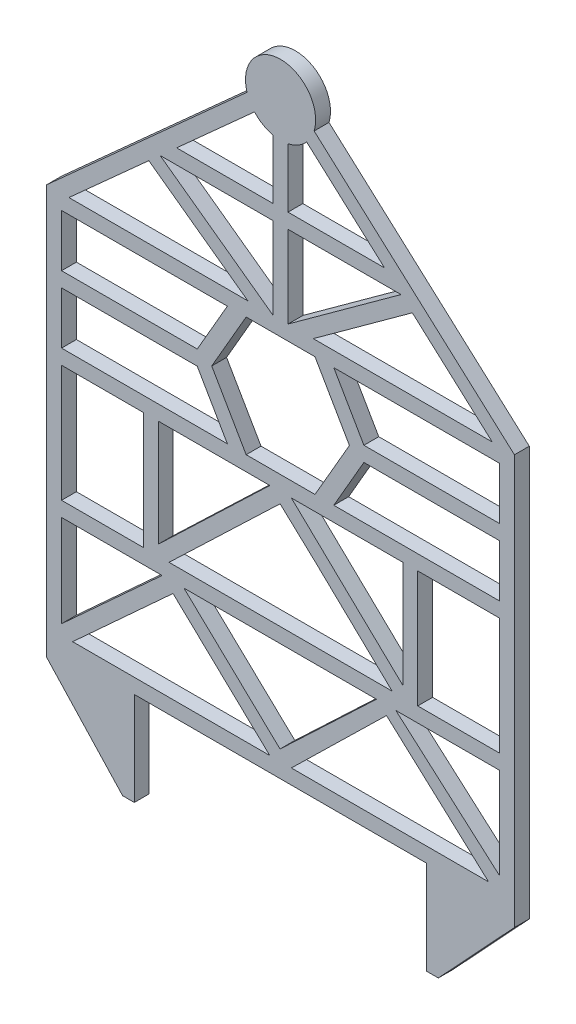
SolidWorks part; units mm, degrees
ref_plane "Front Plane" through (0, 0, 0) normal (0, 0, 1) x (1, 0, 0)
ref_plane "Top Plane" through (0, 0, 0) normal (0, 1, 0) x (1, 0, 0)
ref_plane "Right Plane" through (0, 0, 0) normal (1, 0, 0) x (0, 0, -1)
sketch "Sketch2" plane through (0, 0, 0) normal (0, 0, 1) x (1, 0, 0)
  line L0 (-135.0555, -300) -> (-125.0804, -300)
  line L1 (-126.7754, -220) -> (125.5716, -220)
  line L2 (-125.0804, -220) -> (-125.0804, -300)
  line L3 (-182.114, 120.0492) -> (182.114, 120.0492)
  line L4 (-200, 120.0492) -> (0, 300)
  line L5 (0, 300) -> (200, 120.0492)
  line L6 (-200, 120.0492) -> (-200, -220)
  line L7 (-104.6, 5.4) -> (-117.3, 5.4)
  line L8 (200, 120.0492) -> (200, -220)
  line L9 (124.9196, -220) -> (124.9196, -300)
  line L10 (58.8789, 56.3746) -> (29.4395, 107.3652)
  line L11 (29.4395, 107.3652) -> (-29.4395, 107.3652)
  line L12 (200, -230.0445) -> (134.9116, -300)
  line L13 (-29.4395, 107.3652) -> (-58.8789, 56.3746)
  line L14 (-200, -230.0445) -> (-135.0555, -300)
  line L15 (-104.6, 5.4) -> (104.6, 5.4)
  line L16 (-187.3, -107.3) -> (187.3, -107.3)
  line L17 (124.9196, -300) -> (134.9116, -300)
  line L18 (200, -220) -> (200, -230.0445)
  line L19 (-200, -220) -> (-200, -230.0445)
  line L20 (-58.8789, 56.3746) -> (-29.4395, 5.3839)
  line L21 (-29.4395, 5.3839) -> (29.4395, 5.3839)
  line L22 (187.3101, 107.3492) -> (-187.3356, 107.3492)
  line L23 (-187.3, 107.3492) -> (-187.3, -207.3409)
  line L24 (187.3, -198.4051) -> (187.3, 107.3492)
  line L25 (178.238, -207.3) -> (-178.1968, -207.3)
  line L26 (-181.0126, 120.0492) -> (0, 282.916)
  line L27 (0, 282.916) -> (181.0126, 120.0492)
  line L28 (-191.5054, 110.6082) -> (0, 282.916) construction
  line L29 (0, 282.916) -> (191.5054, 110.6082) construction
  line L31 (0, 202.9179) -> (88.9111, 202.9179)
  line L32 (0, 202.9179) -> (-88.9111, 202.9179)
  line L34 (-103.0261, 190.2179) -> (103.0261, 190.2179)
  line L37 (-6.35, 277.2025) -> (-6.35, 120.0492)
  line L38 (6.35, 277.2025) -> (6.35, 120.0492)
  line L39 (-6.35, 120.0492) -> (-103.0261, 190.2179)
  line L40 (6.35, 120.0492) -> (103.0261, 190.2179)
  line L43 (-117.3, -7.3) -> (-187.3, -7.3)
  line L44 (112.6797, 181.532) -> (27.9708, 120.0492)
  line L45 (-135.0555, -7.3) -> (-135.0555, 5.4)
  line L46 (-27.9708, 120.0492) -> (-112.6797, 181.532)
  line L47 (-117.3, -107.3) -> (-117.3, -7.3)
  line L48 (117.3, -107.3) -> (117.3, -7.3)
  line L49 (117.3, -7.3) -> (187.3, -7.3)
  line L50 (187.3, 5.4) -> (117.3, 5.4)
  line L52 (-187.3, 5.4) -> (-117.3, 5.4)
  line L53 (-117.3, 5.4) -> (-117.3, -7.3)
  line L54 (117.3, -6.6639) -> (117.3, -7.3)
  line L57 (-104.6, 5.4) -> (-104.6, -99.4267)
  line L58 (117.3, 5.4) -> (104.6, 5.4)
  line L59 (104.6, -6.7751) -> (104.6, -99.0643)
  line L60 (-187.3, -120) -> (187.3, -120)
  line L61 (-104.6, -7.3) -> (104.6, -7.3)
  line L62 (29.4395, 5.3839) -> (58.8789, 56.3746)
  line L63 (74.9313, 56.3746) -> (44.9996, 108.2179)
  line L65 (-45.5011, 107.3492) -> (-74.9313, 56.3746)
  line L66 (-74.9313, 56.3746) -> (-37.4657, -8.5179)
  line L68 (-67.7141, -80.8212) -> (-95.4109, -107.3)
  line L69 (-76.4902, -71.6414) -> (-104.6, -98.515)
  line L70 (-104.6, -98.515) -> (-9.1891, -7.3)
  line L71 (30.2421, -44.9971) -> (95.4109, -107.3)
  line L72 (39.0182, -35.8173) -> (104.6, -98.515)
  line L73 (39.0182, -35.8173) -> (9.1891, -7.3)
  line L74 (-67.7141, -80.8212) -> (-0.413, -16.4798)
  line L75 (-0.413, -16.4798) -> (30.2421, -44.9971)
  line L76 (30.2421, -44.9971) -> (-0.413, -16.4798)
  line L79 (37.4657, -8.5179) -> (74.9313, 56.3746)
  line L85 (-187.3, 62.7246) -> (-71.2652, 62.7246)
  line L86 (-187.3, 50.0246) -> (-71.2652, 50.0246)
  line L87 (187.3, 62.7246) -> (71.2652, 62.7246)
  line L88 (187.3, 50.0246) -> (71.2652, 50.0246)
  line L89 (-143.8879, -158.9869) -> (-101.3037, -120)
  line L90 (-101.3037, -120) -> (-187.3, -198.7316)
  line L91 (-135.3121, -168.3541) -> (-177.8516, -207.3)
  line L92 (-177.8516, -207.3) -> (-91.9799, -128.6825)
  line L93 (-28.5576, -188.9302) -> (-91.9799, -128.6825)
  line L94 (-91.9799, -128.6825) -> (-9.2199, -207.3)
  line L95 (-19.8107, -179.7225) -> (-82.6801, -120)
  line L96 (-82.6801, -120) -> (-0.473, -198.0923)
  line L97 (-0.473, -198.0923) -> (82.0151, -120)
  line L98 (161.5818, -192.3729) -> (90.2124, -127.4562)
  line L99 (177.8939, -207.3) -> (161.5818, -192.3729)
  line L100 (170.1555, -183.0037) -> (187.3, -198.0923)
  line L101 (187.3, -198.0923) -> (98.567, -120)
  line L102 (91.1267, -127.2673) -> (9.1891, -207.3)
  line L104 (-37.4657, -8.5179) -> (37.4657, -8.5179) [skipped]
  line L105 (37.4657, 121.267) -> (-37.4657, 121.267) [skipped]
  circle A0 centre (0, 282.916) radius 30
  circle A1 centre (0, 56.3746) radius 64.8924 construction
  circle A2 centre (0, 56.3746) radius 50.9906 construction
  point P4 (0, 0)
  point P7 (0, 0)
  point P9 (-0.0804, -122.4955)
  point P12 (0, 120.0492)
  point P53 (0, 219.3042)
  point P103 (-72.1022, -76.2313)
  point P106 (34.6301, -40.4072)
  point P115 (-139.6, -163.6705)
  point P117 (0, 0)
  point P118 (45.95, -163.65)
  point P119 (-112.6797, 56.3746)
  point P122 (0, 0)
  point P123 (-24.1841, -184.3264)
  point P124 (0, 0)
  point P126 (155.4287, 56.3746)
  point P135 (165.8686, -187.6883)
  point P139 (0, 0)
  point P145 (0, 0)
  point P149 (0, 0)
  dimension "D8" = 60
  dimension "D2" = 12.7
  dimension "D3" = 12.7
  dimension "D11" = 12.7
  dimension "D16" = 12.7
  dimension "D17" = 12.7
  dimension "D19" = 12.7
extrude "Boss-Extrude3" add sketch "Sketch2" along normal blind 12.7
